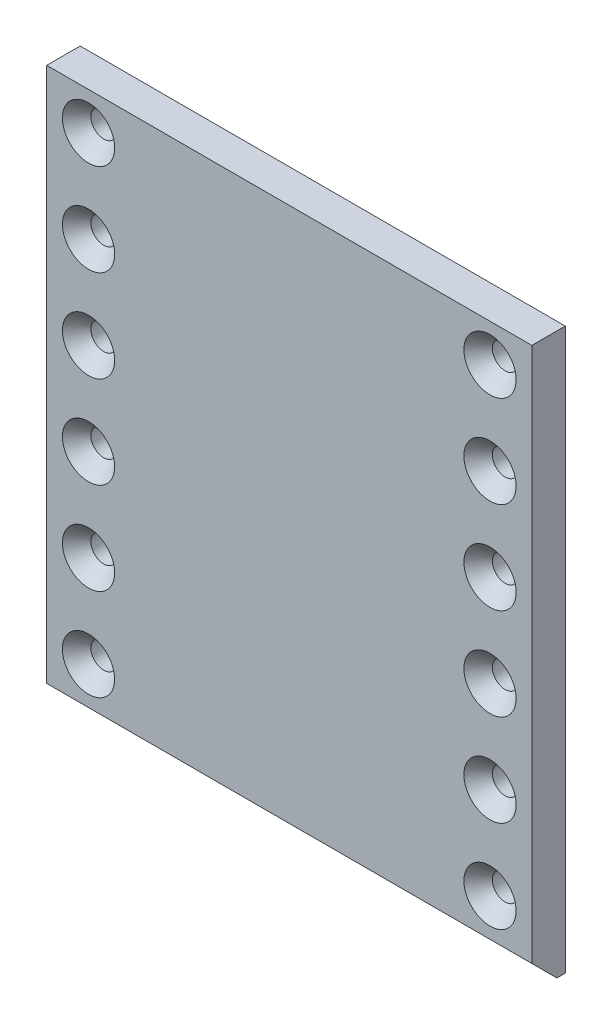
SolidWorks part; units mm, degrees
ref_plane "Front Plane" through (0, 0, 0) normal (0, 0, 1) x (1, 0, 0)
ref_plane "Top Plane" through (0, 0, 0) normal (0, 1, 0) x (1, 0, 0)
ref_plane "Right Plane" through (0, 0, 0) normal (1, 0, 0) x (0, 0, -1)
sketch "Sketch1" plane through (0, 0, 0) normal (0, 0, 1) x (1, 0, 0)
  line L1 (-92.075, 106.3625) -> (92.075, 106.3625)
  line L2 (-92.075, 106.3625) -> (-92.075, -106.3625)
  line L3 (-92.075, -106.3625) -> (92.075, -106.3625)
  line L4 (92.075, 106.3625) -> (92.075, -106.3625)
  line L5 (-92.075, 106.3625) -> (92.075, -106.3625) construction
  line L6 (-92.075, -106.3625) -> (92.075, 106.3625) construction
  point P0 (0, 0)
  dimension "D1" = 184.15
  dimension "D2" = 212.725
extrude "Boss-Extrude1" add sketch "Sketch1" along normal mid plane 12.7
sketch "Sketch2" plane through (0, 0, 6.35) normal (0, 0, 1) x (1, 0, 0)
  line L0 (0, 106.3625) -> (0, -106.3625) construction
  line L1 (92.075, 106.3625) -> (-92.075, 106.3625) construction
  line L2 (-92.075, -106.3625) -> (92.075, -106.3625) construction
sketch "Sketch3" plane through (0, 0, -6.35) normal (0, 0, -1) x (-1, 0, 0)
  line L0 (0, 106.3625) -> (0, -106.3625) construction
  line L1 (-92.075, 106.3625) -> (92.075, 106.3625) construction
  line L2 (92.075, -106.3625) -> (-92.075, -106.3625) construction
hole_wizard "CSK for 3/8 Flat Head Socket Cap Screw1" positions "Sketch7" profile "Sketch6" countersink size "3/8" standard "ANSI Inch" end condition through all
sketch "Sketch7" plane through (0, 0, 6.35) normal (0, 0, 1) x (1, 0, 0)
  line L0 (-76.2, 92.075) -> (76.2, 92.075) construction
  line L1 (0, 92.075) -> (0, 106.3625) construction
  line L2 (92.075, 106.3625) -> (-92.075, 106.3625) construction
  line L3 (-76.2, -82.55) -> (76.2, -82.55) construction
  line L4 (76.2, -82.55) -> (76.2, 92.075) construction
  line L5 (-76.2, 92.075) -> (-76.2, -82.55) construction
  line L6 (-76.2, 57.15) -> (76.2, 57.15) construction
  line L7 (-76.2, 22.225) -> (76.2, 22.225) construction
  line L8 (-76.2, -12.7) -> (76.2, -12.7) construction
  line L9 (-76.2, -47.625) -> (76.2, -47.625) construction
  line L10 (-92.075, -106.3625) -> (92.075, -106.3625) construction
  point P0 (-76.2, 92.075)
  point P2 (-76.2, 57.15)
  point P4 (-76.2, 22.225)
  point P6 (-76.2, -12.7)
  point P8 (-76.2, -47.625)
  point P10 (-76.2, -82.55)
  point P12 (76.2, -82.55)
  point P14 (76.2, -47.625)
  point P16 (76.2, -12.7)
  point P18 (76.2, 22.225)
  point P20 (76.2, 57.15)
  point P22 (76.2, 92.075)
  dimension "D1" = 152.4
  dimension "D2" = 174.625
  dimension "D3" = 14.2875
  dimension "D4" = 34.925
  dimension "D5" = 34.925
  dimension "D6" = 34.925
  dimension "D7" = 34.925
  dimension "D8" = 34.925
  dimension "D9" = 23.8125
sketch "Sketch6" plane through (-76.2, 92.075, 6.35) normal (1, 0, 0) x (0, -1, 0)
  line L0 (0, 0) -> (0, 12.7)
  line L1 (0, 12.7) -> (4.9022, 12.7)
  line L2 (4.9022, 12.7) -> (4.9022, 5.7708)
  line L3 (4.9022, 5.7708) -> (9.9187, 0)
  line L5 (9.9187, 0) -> (0, 0)
  line L6 (-4.9022, 5.7708) -> (-9.9187, 0) construction
  line L11 (0, -6.35) -> (0, 107.95) construction
  dimension "Thru Hole Dia." = 9.8044
  dimension "Thru Hole Depth" = 12.7
  dimension "Near C'Sink Dia." = 19.8374
  dimension "Near C'Sink Angle" = 82
chamfer "Chamfer1" distance 9.525 angle 45 1 edges at (0, -106.3625, 6.35)
